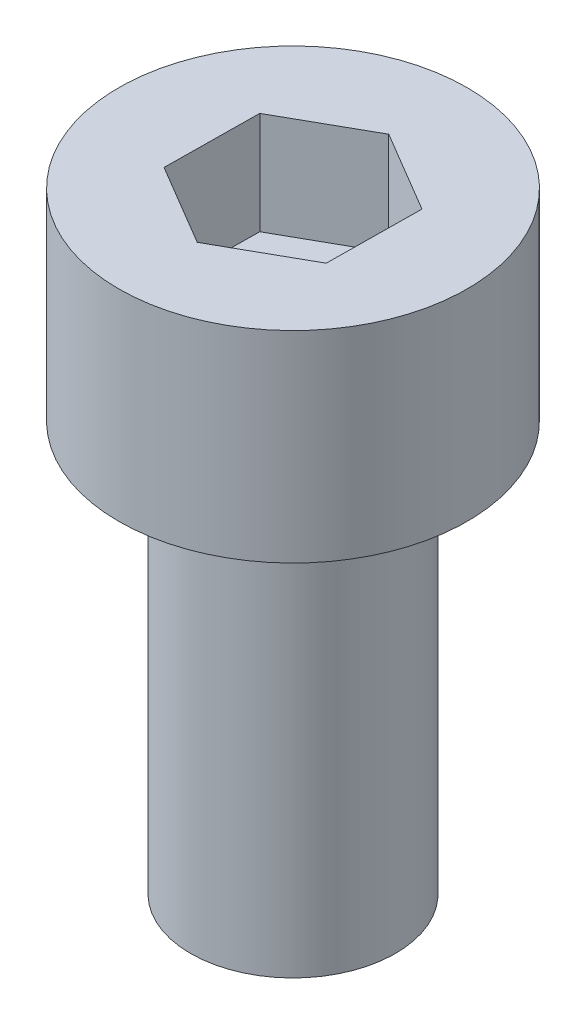
SolidWorks part; units mm, degrees
ref_plane "前视基准面" through (0, 0, 0) normal (0, 0, 1) x (1, 0, 0)
ref_plane "上视基准面" through (0, 0, 0) normal (0, 1, 0) x (1, 0, 0)
ref_plane "右视基准面" through (0, 0, 0) normal (1, 0, 0) x (0, 0, -1)
sketch "草图1" plane through (0, 0, 0) normal (0, 1, 0) x (1, 0, 0)
  circle A0 centre (0, 0) radius 2.5
  dimension "D1" = 5
extrude "凸台-拉伸1" add sketch "草图1" along normal blind 10
sketch "草图2" plane through (0, 10, 0) normal (0, 1, 0) x (1, 0, 0)
  circle A0 centre (0, 0) radius 4.25
  dimension "D1" = 8.5
extrude "凸台-拉伸2" add sketch "草图2" along normal blind 4.91
sketch "草图3" plane through (0, 14.91, 0) normal (0, 1, 0) x (1, 0, 0)
  line L1 (1.9872, -1.1765) -> (2.0125, 1.1327)
  line L2 (2.0125, 1.1327) -> (0.0253, 2.3093)
  line L3 (0.0253, 2.3093) -> (-1.9872, 1.1765)
  line L4 (-1.9872, 1.1765) -> (-2.0125, -1.1327)
  line L5 (-2.0125, -1.1327) -> (-0.0253, -2.3093)
  line L6 (-0.0253, -2.3093) -> (1.9872, -1.1765)
  circle A0 centre (0, 0) radius 2 construction
  dimension "D1" = 4
extrude "切除-拉伸1" cut sketch "草图3" against normal blind 2.5
